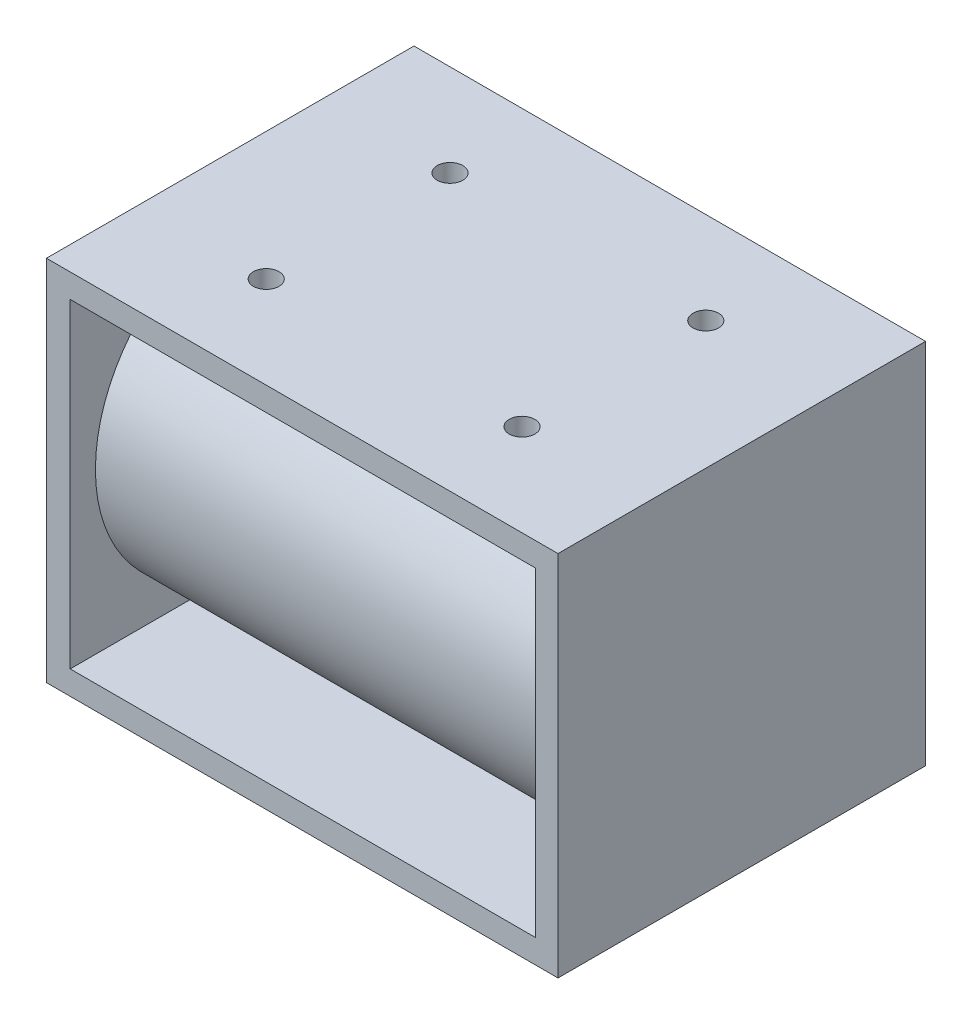
SolidWorks part; units mm, degrees
ref_plane "Front Plane" through (0, 0, 0) normal (0, 0, 1) x (1, 0, 0)
ref_plane "Top Plane" through (0, 0, 0) normal (0, 1, 0) x (1, 0, 0)
ref_plane "Right Plane" through (0, 0, 0) normal (1, 0, 0) x (0, 0, -1)
sketch "Sketch1" plane through (0, 0, 0) normal (0, 0, 1) x (1, 0, 0)
  line L1 (0, 0) -> (50.8, 0)
  line L2 (0, 0) -> (0, 36.4998)
  line L3 (0, 36.4998) -> (50.8, 36.4998)
  line L4 (50.8, 0) -> (50.8, 36.4998)
  line L5 (2.3622, 2.3622) -> (48.5655, 2.3622)
  line L6 (2.3622, 2.3622) -> (2.3622, 34.1376)
  line L7 (2.3622, 34.1376) -> (48.5655, 34.1376)
  line L8 (48.5655, 2.3622) -> (48.5655, 34.1376)
extrude "Boss-Extrude1" add sketch "Sketch1" along normal blind 36.4998
ref_plane "Plane2" through (50.8, 0, 0) normal (1, 0, 0) x (0, 0, -1)
ref_plane "Plane6" through (0, 0, 0) normal (-1, 0, 0) x (0, 0, 1)
ref_plane "Plane10" through (2.3622, 0, 0) normal (1, 0, 0) x (0, 0, -1)
sketch "Sketch8" plane through (2.3622, 0, 0) normal (1, 0, 0) x (0, 0, -1)
  line L0 (-18.2499, 2.3622) -> (-18.2499, 34.1376) construction
  line L1 (-36.4998, 2.3622) -> (0, 2.3622) construction
  line L2 (-36.4998, 34.1376) -> (0, 34.1376) construction
  circle A0 centre (-18.2499, 18.2499) radius 15.748
extrude "Boss-Extrude3" add sketch "Sketch8" along normal blind 46.0756
sketch "Sketch9" plane through (0, 0, 0) normal (-1, 0, 0) x (0, 0, 1)
  line L0 (18.2499, 36.4998) -> (18.2499, 0) construction
  line L1 (36.4998, 36.4998) -> (0, 36.4998) construction
  line L2 (36.4998, 0) -> (0, 0) construction
  line L3 (0, 18.2499) -> (36.4998, 18.2499) construction
  line L4 (0, 36.4998) -> (0, 0) construction
  line L5 (36.4998, 36.4998) -> (36.4998, 0) construction
  circle A0 centre (18.2499, 18.2499) radius 5.5499
  point P12 (18.2499, 18.2499)
extrude "Cut-Extrude1" cut sketch "Sketch9" against normal blind 25.4
ref_plane "Plane11" through (0, 36.4998, 0) normal (0, 1, 0) x (1, 0, 0)
sketch "Sketch10" plane through (0, 36.4998, 0) normal (0, 1, 0) x (1, 0, 0)
  line L0 (25.4, 0) -> (25.4, -36.4998) construction
  line L1 (50.8, 0) -> (0, 0) construction
  line L2 (50.8, -36.4998) -> (0, -36.4998) construction
  line L3 (25.4, -18.2499) -> (50.8, -18.2499) construction
  line L4 (50.8, -20.0749) -> (50.8, 20.0749) construction
  line L5 (25.4, -18.2499) -> (0, -18.2499) construction
  line L6 (0, 20.0749) -> (0, -20.0749) construction
  line L7 (38.1, -9.125) -> (38.1, -18.2499) construction
  line L8 (38.1, -9.125) -> (25.4, -9.125) construction
  circle A0 centre (38.1, -9.125) radius 1.27
  circle A1 centre (12.7, -9.125) radius 1.27
  circle A2 centre (38.1, -27.3748) radius 1.27
  circle A3 centre (12.7, -27.3748) radius 1.27
  point P14 (25.4, -18.2499)
extrude "Cut-Extrude2" cut sketch "Sketch10" against normal up to next
